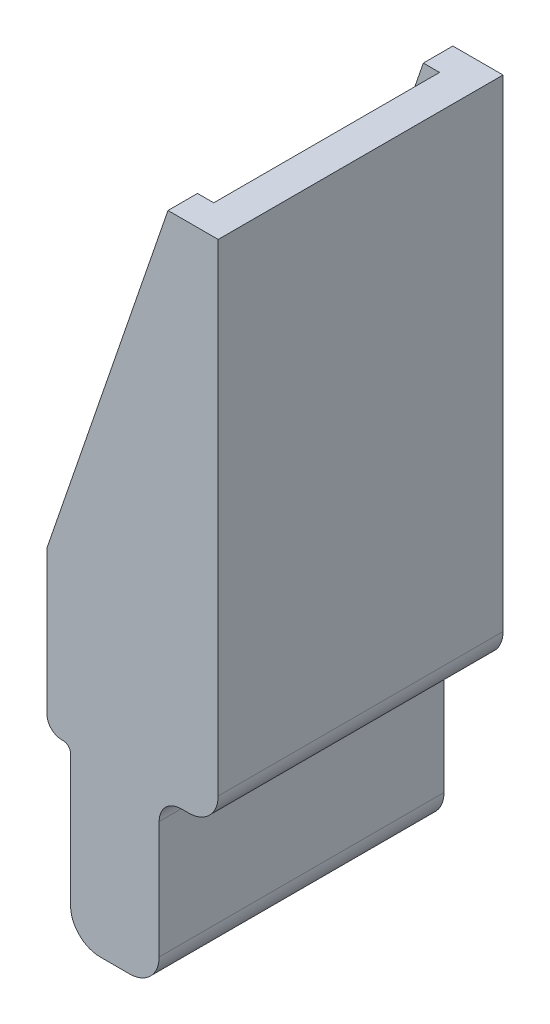
SolidWorks part; units mm, degrees
ref_plane "Alzado" through (0, 0, 0) normal (0, 0, 1) x (1, 0, 0)
ref_plane "Planta" through (0, 0, 0) normal (0, 1, 0) x (1, 0, 0)
ref_plane "Vista lateral" through (0, 0, 0) normal (1, 0, 0) x (0, 0, -1)
sketch "Croquis1" plane through (0, 0, 0) normal (0, 0, 1) x (1, 0, 0)
  line L0 (5.8, 23.05) -> (2.4, 23.05)
  line L2 (2.4, 23.05) -> (-5.8, -0.85)
  line L9 (1.8, -13.107) -> (1.8, -21.05)
  line L10 (-0.2, -23.05) -> (-2.2, -23.05)
  line L11 (-4.2, -21.05) -> (-4.2, -12.1093)
  line L12 (-4.7023, -11.6093) -> (-4.7953, -11.6097)
  line L13 (-5.8, -10.6097) -> (-5.8, -0.85)
  line L14 (3.3, -11.607) -> (3.8, -11.607)
  line L15 (5.8, -9.607) -> (5.8, 23.05)
  arc A0 (3.8, -11.607) -> (5.8, -9.607) centre (3.8, -9.607) ccw
  arc A1 (1.8, -13.107) -> (3.3, -11.607) centre (3.3, -13.107) cw
  arc A2 (1.8, -21.05) -> (-0.2, -23.05) centre (-0.2, -21.05) cw
  arc A3 (-2.2, -23.05) -> (-4.2, -21.05) centre (-2.2, -21.05) cw
  arc A4 (-4.7953, -11.6097) -> (-5.8, -10.6097) centre (-4.8, -10.6097) cw
  arc A5 (-4.2, -12.1093) -> (-4.7023, -11.6093) centre (-4.7, -12.1093) ccw
  point P0 (0, 0)
  dimension "D1" = 2
  dimension "D2" = 1.5
  dimension "D3" = 1
  dimension "D4" = 1.8
  dimension "D5" = 2.4
  dimension "D6" = 4.7023
  dimension "D7" = 4.7953
  dimension "D8" = 23.05
  dimension "D9" = 0.85
  dimension "D10" = 10.6097
  dimension "D11" = 11.607
  dimension "D12" = 23.05
extrude "Saliente-Extruir1" add sketch "Croquis1" along normal blind 19.3
sketch "Croquis2" plane through (-5.8, 0, 0) normal (-1, 0, 0) x (0, 0, 1)
  line L0 (0, -0.85) -> (0, -10.6097) construction
  line L1 (19.3, 23.05) -> (0, 23.05) construction
  line L2 (19.3, -10.6097) -> (0, -10.6097) construction
  line L3 (17.3, -3.25) -> (17.3, 23.05)
  line L4 (2, -3.25) -> (17.3, -3.25)
  line L5 (17.3, 23.05) -> (2, 23.05)
  line L6 (2, 23.05) -> (2, -3.25)
  dimension "D1" = 2
  dimension "D2" = 17.3
  dimension "D3" = 7.3597
extrude "Cortar-Extruir1" cut sketch "Croquis2" against normal blind 9.3 contours L3 L5 L6 L4
